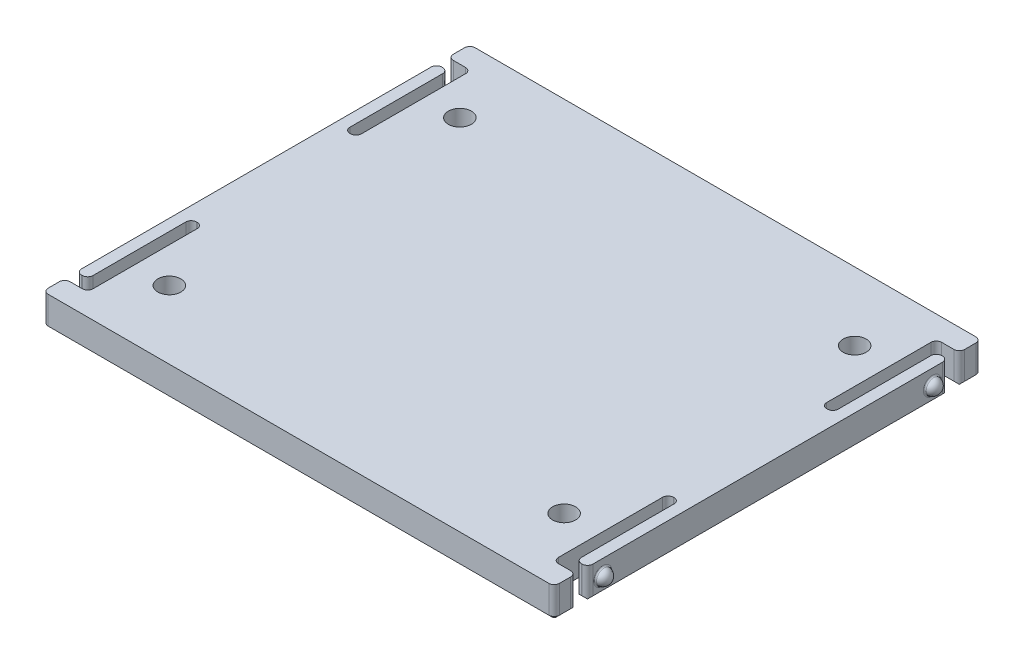
SolidWorks part; units mm, degrees
ref_plane "Front Plane" through (0, 0, 0) normal (0, 0, 1) x (1, 0, 0)
ref_plane "Top Plane" through (0, 0, 0) normal (0, 1, 0) x (1, 0, 0)
ref_plane "Right Plane" through (0, 0, 0) normal (1, 0, 0) x (0, 0, -1)
sketch "Sketch1" plane through (0, 0, 0) normal (0, 1, 0) x (1, 0, 0)
  line L5 (-33.35, 25) -> (-30.35, 25)
  line L6 (-32.65, -27.85) -> (32.65, -27.85)
  line L11 (-33.35, -27.15) -> (-33.35, -25)
  line L12 (-32.65, 27.85) -> (32.65, 27.85)
  line L13 (33.35, -27.15) -> (33.35, -25)
  line L14 (-33.35, -27.85) -> (33.35, 27.85) construction
  line L15 (-33.35, 27.85) -> (33.35, -27.85) construction
  line L16 (-30.35, 25) -> (-30.35, 10)
  line L17 (-30.35, 10) -> (-31.85, 10)
  line L18 (-31.85, 10) -> (-31.85, 23.5)
  line L19 (-31.85, 23.5) -> (-33.35, 23.5)
  line L21 (-33.35, 0) -> (33.35, 0) construction
  line L22 (0, 27.85) -> (0, -27.85) construction
  line L23 (31.85, 23.5) -> (33.35, 23.5)
  line L24 (31.85, 10) -> (31.85, 23.5)
  line L25 (30.35, 10) -> (31.85, 10)
  line L26 (30.35, 25) -> (30.35, 10)
  line L27 (33.35, 25) -> (30.35, 25)
  line L29 (31.85, -10) -> (31.85, -23.5)
  line L30 (30.35, -10) -> (31.85, -10)
  line L31 (30.35, -25) -> (30.35, -10)
  line L32 (33.35, -25) -> (30.35, -25)
  line L34 (31.85, -23.5) -> (33.35, -23.5)
  line L35 (-31.85, -23.5) -> (-33.35, -23.5)
  line L36 (-31.85, -10) -> (-31.85, -23.5)
  line L37 (-30.35, -10) -> (-31.85, -10)
  line L38 (-30.35, -25) -> (-30.35, -10)
  line L39 (-33.35, -25) -> (-30.35, -25)
  line L41 (-33.35, 25) -> (-33.35, 27.15)
  line L42 (-33.35, -23.5) -> (-33.35, 23.5)
  line L43 (33.35, -23.5) -> (33.35, 23.5)
  line L44 (33.35, 25) -> (33.35, 27.15)
  arc A1 (-32.65, -27.85) -> (-33.35, -27.15) centre (-32.65, -27.15) cw
  arc A2 (32.65, -27.85) -> (33.35, -27.15) centre (32.65, -27.15) ccw
  arc A3 (32.65, 27.85) -> (33.35, 27.15) centre (32.65, 27.15) cw
  arc A4 (-33.35, 27.15) -> (-32.65, 27.85) centre (-32.65, 27.15) cw
  point P0 (0, 0)
  point P47 (0, 0)
  dimension "D5" = 10
  dimension "D3" = 0.7
  dimension "D1" = 66.7
  dimension "D2" = 55.7
  dimension "D4" = 1.5
  dimension "D6" = 15
  dimension "D7" = 1.5
  dimension "D8" = 1.5
extrude "Boss-Extrude1" add sketch "Sketch1" along normal blind 4
sketch "Sketch3" plane through (0, 4, 0) normal (0, 1, 0) x (1, 0, 0)
  line L1 (-25.75, -18.95) -> (25.75, -18.95) construction
  line L2 (-25.75, -18.95) -> (-25.75, 18.95) construction
  line L3 (-25.75, 18.95) -> (25.75, 18.95) construction
  line L4 (25.75, -18.95) -> (25.75, 18.95) construction
  line L5 (-25.75, -18.95) -> (25.75, 18.95) construction
  line L6 (-25.75, 18.95) -> (25.75, -18.95) construction
  circle A0 centre (-25.75, 18.95) radius 1.5
  circle A1 centre (25.75, 18.95) radius 1.5
  circle A2 centre (25.75, -18.95) radius 1.5
  circle A3 centre (-25.75, -18.95) radius 1.5
  point P0 (0, 0)
  dimension "D1" = 3
  dimension "D2" = 51.5
  dimension "D3" = 37.9
extrude "Cut-Extrude2" cut sketch "Sketch3" against normal through all
ref_plane "Plane1" through (0, 2, 0) normal (0, 1, 0) x (1, 0, 0)
sketch "Sketch5" plane through (0, 2, 0) normal (0, 1, 0) x (1, 0, 0)
  line L0 (-33.35, 23.5) -> (-33.35, -23.5) construction
  line L1 (-34.35, 21.5) -> (-33.35, 21.5)
  line L2 (-31.85, 23.5) -> (-33.35, 23.5) construction
  line L3 (-33.35, 20.5) -> (-33.35, 21.5)
  arc A0 (-33.35, 20.5) -> (-34.35, 21.5) centre (-33.35, 21.5) cw
  dimension "D1" = 1
  dimension "D2" = 2
revolve "Revolve1" add sketch "Sketch5" angle 360 about L1
mirror "Mirror1" about plane through (0, 0, 0) normal (0, 0, 1) of "Revolve1"
mirror "Mirror2" about plane through (0, 0, 0) normal (1, 0, 0) of "Mirror1", "Revolve1"
chamfer "Chamfer1" distance 0.4 angle 45 36 edges at (-31.85, 0, -25) (-30.35, 0, -17.5) (-31.1, 0, -10) (-31.85, 0, -16.75) (-32.6, 0, -23.5) (-33.35, 0, 0) (-32.6, 0, 23.5) (-31.85, 0, 16.75) (-31.1, 0, 10) (-30.35, 0, 17.5) (-31.85, 0, 25) (-33.35, 0, 26.075) (-33.145, 0, 27.645) (0, 0, 27.85) (33.145, 0, 27.645) (33.35, 0, 26.075) (31.85, 0, 25) (30.35, 0, 17.5) (31.1, 0, 10) (31.85, 0, 16.75) (32.6, 0, 23.5) (33.35, 0, 0) (32.6, 0, -23.5) (31.85, 0, -16.75) (31.1, 0, -10) (30.35, 0, -17.5) (31.85, 0, -25) (33.35, 0, -26.075) (33.145, 0, -27.645) (0, 0, -27.85) (-33.145, 0, -27.645) (-33.35, 0, -26.075) (-25.75, 0, -17.45) (25.75, 0, -17.45) (25.75, 0, 20.45) (-25.75, 0, 20.45)
fillet "Fillet1" radius 0.7 24 edges at (30.35, 2.2, 25) (33.35, 2.2, 25) (33.35, 2.2, 23.5) (31.85, 2.2, 23.5) (31.85, 2.2, 10) (30.35, 2.2, 10) (31.85, 2.2, -10) (30.35, 2.2, -10) (30.35, 2.2, -25) (33.35, 2.2, -25) (31.85, 2.2, -23.5) (33.35, 2.2, -23.5) (-33.35, 2.2, 25) (-30.35, 2.2, 25) (-33.35, 2.2, 23.5) (-31.85, 2.2, 23.5) (-31.85, 2.2, 10) (-30.35, 2.2, 10) (-33.35, 2.2, -23.5) (-31.85, 2.2, -23.5) (-31.85, 2.2, -10) (-30.35, 2.2, -10) (-30.35, 2.2, -25) (-33.35, 2.2, -25)
fillet "Fillet2" radius 0.2 4 edges at (33.35, 2, -20.5) (33.35, 2, 20.5) (-33.35, 2, 20.5) (-33.35, 2, -20.5)
